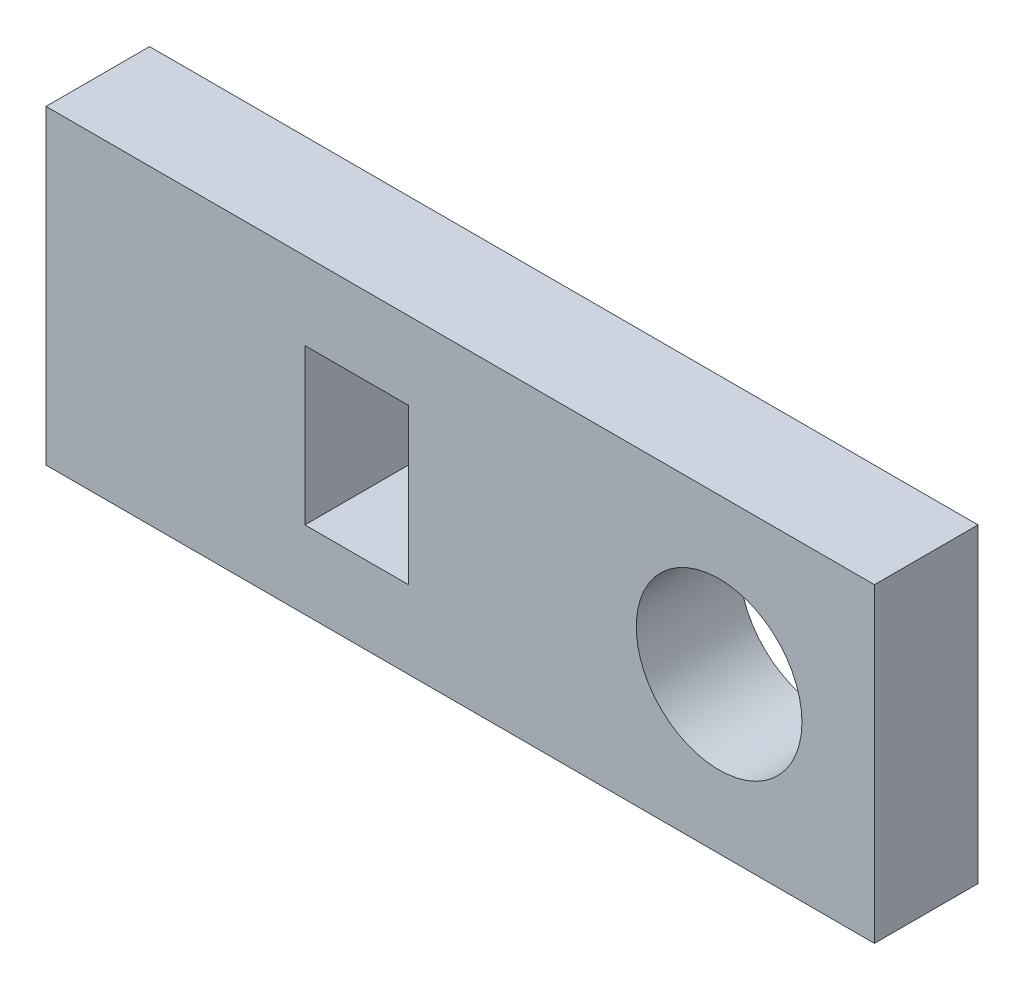
SolidWorks part; units mm, degrees
material "Acrylic (Medium-high impact)"
ref_plane "Front Plane" through (0, 0, 0) normal (0, 0, 1) x (1, 0, 0)
ref_plane "Top Plane" through (0, 0, 0) normal (0, 1, 0) x (1, 0, 0)
ref_plane "Right Plane" through (0, 0, 0) normal (1, 0, 0) x (0, 0, -1)
sketch "Sketch1" plane through (0, 0, 0) normal (0, 0, 1) x (1, 0, 0)
  line L1 (0, 0) -> (40, 0)
  line L2 (0, 0) -> (0, 15)
  line L3 (0, 15) -> (40, 15)
  line L4 (40, 0) -> (40, 15)
  line L5 (12.5, 11.25) -> (17.5, 11.25)
  line L6 (12.5, 11.25) -> (12.5, 3.75)
  line L7 (12.5, 3.75) -> (17.5, 3.75)
  line L8 (17.5, 11.25) -> (17.5, 3.75)
  circle A0 centre (32.5, 7.5) radius 4
  point P8 (0, 7.5)
  point P12 (12.5, 7.5)
  dimension "D1" = 8
  dimension "D2" = 40
  dimension "D3" = 15
  dimension "D4" = 5
  dimension "D5" = 7.5
  dimension "D6" = 7.5
  dimension "D7" = 15
extrude "Boss-Extrude1" add sketch "Sketch1" along normal blind 5
